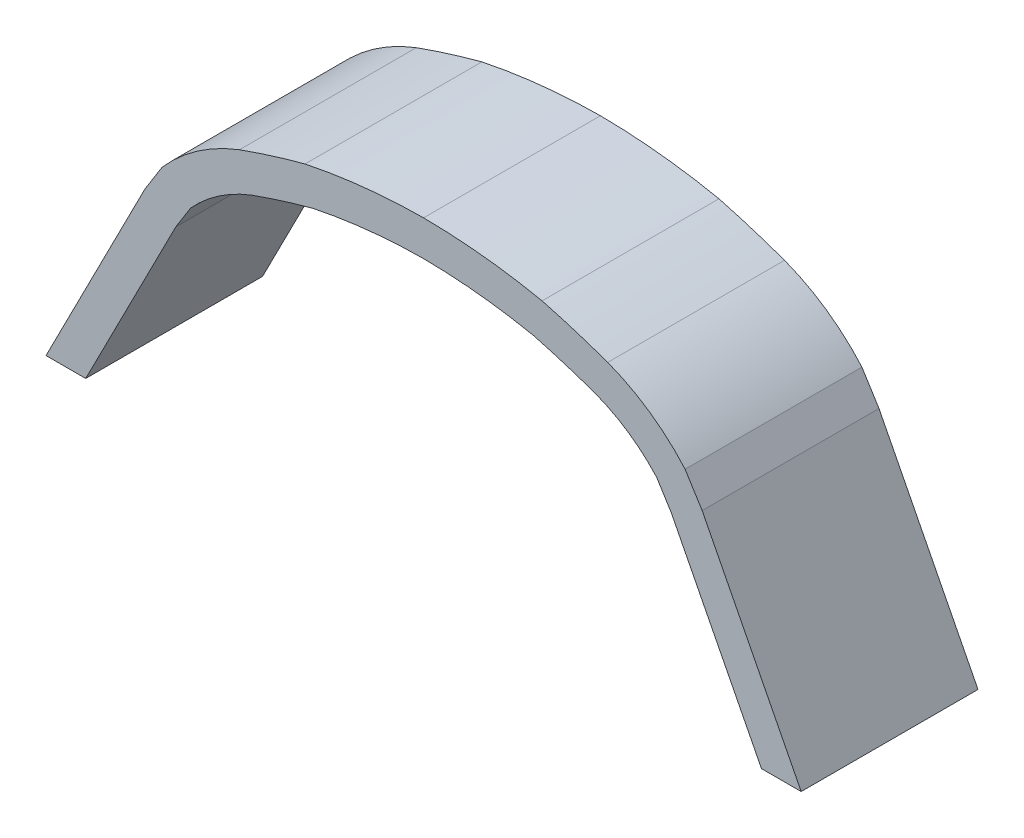
SolidWorks part; units mm, degrees
ref_plane "Front Plane" through (0, 0, 0) normal (0, 0, 1) x (1, 0, 0)
ref_plane "Top Plane" through (0, 0, 0) normal (0, 1, 0) x (1, 0, 0)
ref_plane "Right Plane" through (0, 0, 0) normal (1, 0, 0) x (0, 0, -1)
sketch "Sketch1" plane through (0, 0, 0) normal (0, 0, 1) x (1, 0, 0)
  line L0 (-4.7635, 0) -> (4.7635, 0) construction
  line L1 (-4.7635, 0) -> (-4.8535, 0) construction
  line L2 (-4.8535, 0) -> (-3.5592, 2.5338)
  line L3 (0, 0) -> (0, 3.9174) construction
  line L4 (-4.8002, 0.1044) -> (-4.7311, 0.0723) construction
  line L5 (-3.5592, 2.5338) -> (-3.3482, 2.8713)
  line L6 (-3.5592, 2.5338) -> (-3.4941, 2.4941) construction
  line L7 (-2.905, 3.159) -> (-2.9441, 3.2244) construction
  line L8 (-2.4359, 3.4045) -> (-2.4687, 3.4733) construction
  line L9 (-2.0073, 3.548) -> (-2.0301, 3.6207) construction
  line L10 (-1.5693, 3.675) -> (-1.5857, 3.7495) construction
  line L11 (-0.7917, 3.8061) -> (-0.7969, 3.8722) construction
  line L12 (3.5592, 2.5338) -> (3.3482, 2.8713)
  line L13 (-3.3482, 2.8713) -> (-3.2837, 2.8308) construction
  line L14 (4.8535, 0) -> (3.5592, 2.5338)
  line L15 (4.7635, 0) -> (4.8535, 0) construction
  line L16 (4.8535, 0) -> (5.4239, 0)
  line L17 (-5.4239, 0) -> (-4.0016, 2.7844)
  line L18 (-4.0016, 2.7844) -> (-3.7564, 3.1767)
  line L19 (4.0016, 2.7844) -> (3.7564, 3.1767)
  line L20 (5.4239, 0) -> (4.0016, 2.7844)
  line L22 (-4.8535, 0) -> (-5.4239, 0)
  line L23 (-5.6834, -0.508) -> (-4.0016, 2.7844) construction
  line L24 (-4.7635, -0.508) -> (-5.6834, -0.508) construction
  line L25 (5.6834, -0.508) -> (4.0016, 2.7844) construction
  line L26 (4.7635, -0.508) -> (5.6834, -0.508) construction
  arc A0 (-3.3482, 2.8713) -> (-2.4687, 3.4733) centre (-1.6554, 1.3414) cw
  arc A1 (-2.4687, 3.4733) -> (-1.5857, 3.7495) centre (1.2481, -6.8605) cw
  arc A2 (-1.5857, 3.7495) -> (0, 3.9174) centre (0.0631, -4.2481) cw
  arc A3 (1.5857, 3.7495) -> (0, 3.9174) centre (-0.0631, -4.2481) ccw
  arc A4 (2.4687, 3.4733) -> (1.5857, 3.7495) centre (-1.2481, -6.8605) ccw
  arc A5 (3.3482, 2.8713) -> (2.4687, 3.4733) centre (1.6554, 1.3414) ccw
  arc A6 (-3.7564, 3.1767) -> (-2.645, 3.9497) centre (-1.6554, 1.3414) cw
  arc A7 (-2.645, 3.9497) -> (-1.7027, 4.244) centre (1.2481, -6.8605) cw
  arc A8 (-1.7027, 4.244) -> (0, 4.4254) centre (0.0631, -4.2481) cw
  arc A9 (1.7027, 4.244) -> (0, 4.4254) centre (-0.0631, -4.2481) ccw
  arc A10 (2.645, 3.9497) -> (1.7027, 4.244) centre (-1.2481, -6.8605) ccw
  arc A11 (3.7564, 3.1767) -> (2.645, 3.9497) centre (1.6554, 1.3414) ccw
  spline S0 degree 3 poles (-4.7635, 0) (-4.7635, 0.0005) (-4.7636, 0.0011) (-4.7636, 0.0019) (-4.7636, 0.0022) (-4.7535, 0.024) (-4.7412, 0.0505) (-4.7267, 0.0817) (-4.7197, 0.0961) (-4.6407, 0.252) (-4.5474, 0.4361) (-4.4398, 0.6484) (-4.3897, 0.747) (-4.2916, 0.9396) (-4.2049, 1.1097) (-4.1297, 1.2572) (-4.1136, 1.288) (-4.0861, 1.339) (-4.0587, 1.39) (-4.0312, 1.441) (-4.0153, 1.4719) (-3.9452, 1.6136) (-3.8676, 1.7705) (-3.7826, 1.9425) (-3.7447, 2.019) (-3.6799, 2.1487) (-3.6232, 2.2623) (-3.5745, 2.3598) (-3.5593, 2.3872) (-3.5321, 2.4317) (-3.505, 2.4763) (-3.4778, 2.5208) (-3.4614, 2.5475) (-3.397, 2.6501) (-3.3343, 2.7501) (-3.2733, 2.8475) (-3.259, 2.8647) (-3.2248, 2.8969) (-3.1954, 2.9245) (-3.1705, 2.948) (-3.1676, 2.9507) (-3.1648, 2.9534) (-3.1625, 2.9556) (-3.161, 2.9569) (-3.1514, 2.9657) (-3.1398, 2.9762) (-3.1264, 2.9885) (-3.119, 2.9948) (-3.1057, 3.0059) (-3.0924, 3.017) (-3.0793, 3.028) (-3.0724, 3.0342) (-3.0633, 3.0446) (-3.0545, 3.0546) (-3.0461, 3.0642) (-3.0403, 3.0695) (-3.0296, 3.0771) (-3.019, 3.0848) (-3.0083, 3.0924) (-3.0021, 3.0968) (-2.9919, 3.1039) (-2.9822, 3.1106) (-2.9731, 3.117) (-2.9684, 3.1202) (-2.9617, 3.1245) (-2.9555, 3.1285) (-2.9497, 3.1322) (-2.9462, 3.1344) (-2.9314, 3.1432) (-2.9121, 3.1547) (-2.8911, 3.1673) (-2.8752, 3.1771) (-2.8603, 3.1863) (-2.846, 3.1952) (-2.8311, 3.204) (-2.8192, 3.2111) (-2.8036, 3.2204) (-2.7932, 3.2266) (-2.7831, 3.2326) (-2.76, 3.2462) (-2.735, 3.2609) (-2.7067, 3.2776) (-2.6923, 3.2852) (-2.6431, 3.3078) (-2.5899, 3.3323) (-2.5327, 3.3586) (-2.5059, 3.3711) (-2.466, 3.3901) (-2.4275, 3.4085) (-2.3904, 3.4262) (-2.3674, 3.4352) (-2.1317, 3.509) (-1.9031, 3.5806) (-1.6818, 3.6498) (-1.6801, 3.6504) (-1.6772, 3.6514) (-1.6744, 3.6524) (-1.6717, 3.6534) (-1.6703, 3.6539) (-1.6682, 3.6545) (-1.6659, 3.6551) (-1.6638, 3.6557) (-1.6619, 3.6562) (-1.6601, 3.6566) (-1.6583, 3.6569) (-1.645, 3.6595) (-1.6294, 3.6625) (-1.6113, 3.6659) (-1.6028, 3.6677) (-1.506, 3.6889) (-1.4084, 3.7104) (-1.3099, 3.732) (-1.2988, 3.7342) (-1.2803, 3.7376) (-1.2618, 3.741) (-1.2432, 3.7445) (-1.2321, 3.7463) (-1.1355, 3.7604) (-1.0223, 3.777) (-0.8926, 3.7959) (-0.8314, 3.803) (-0.7312, 3.8108) (-0.6366, 3.8181) (-0.5475, 3.825) (-0.5026, 3.8285) (-0.4423, 3.8303) (-0.3829, 3.8322) (-0.3245, 3.834) (-0.2825, 3.8351) (-0.201, 3.837) (-0.1153, 3.8391) (-0.0254, 3.8413) (0.0292, 3.8412) (0.1211, 3.8389) (0.2093, 3.8366) (0.2936, 3.8345) (0.3368, 3.8334) (0.3962, 3.8315) (0.4561, 3.8296) (0.5166, 3.8276) (0.5612, 3.8241) (0.6495, 3.8171) (0.7432, 3.8096) (0.8423, 3.8018) (0.9028, 3.7947) (1.0326, 3.7755) (1.145, 3.759) (1.24, 3.7449) (1.2481, 3.7436) (1.2696, 3.7396) (1.2894, 3.7359) (1.3074, 3.7326) (1.3101, 3.732) (1.4049, 3.7112) (1.5019, 3.6898) (1.6008, 3.6681) (1.6097, 3.6662) (1.6286, 3.6626) (1.6448, 3.6595) (1.6586, 3.6568) (1.6604, 3.6564) (1.6623, 3.656) (1.6643, 3.6556) (1.6665, 3.655) (1.6691, 3.6542) (1.6714, 3.6535) (1.7859, 3.6227) (1.9031, 3.5912) (2.0236, 3.5588) (2.0343, 3.5553) (2.0517, 3.5488) (2.0691, 3.5423) (2.0866, 3.5358) (2.097, 3.532) (2.1688, 3.5065) (2.2556, 3.4758) (2.3574, 3.4396) (2.4112, 3.4149) (2.5347, 3.3534) (2.6432, 3.2993) (2.7369, 3.2526) (2.7449, 3.2483) (2.7582, 3.2409) (2.7714, 3.2335) (2.7847, 3.2262) (2.7925, 3.2216) (2.8055, 3.214) (2.8184, 3.2064) (2.8313, 3.1988) (2.8391, 3.1943) (2.8686, 3.1781) (2.8977, 3.1621) (2.9265, 3.1463) (2.9331, 3.1424) (2.9465, 3.1339) (2.9582, 3.1265) (2.9682, 3.1202) (2.9696, 3.1193) (2.972, 3.1177) (2.9744, 3.1161) (2.9768, 3.1145) (2.9782, 3.1136) (2.9847, 3.1089) (2.9923, 3.1035) (3.0007, 3.0974) (3.0049, 3.0944) (3.0199, 3.0836) (3.0363, 3.0718) (3.0541, 3.0589) (3.0624, 3.0527) (3.0749, 3.0427) (3.0872, 3.0329) (3.0992, 3.0232) (3.1061, 3.0163) (3.1171, 3.0036) (3.1278, 2.9912) (3.1382, 2.9792) (3.1437, 2.9729) (3.1524, 2.9648) (3.1621, 2.9558) (3.1714, 2.9471) (3.1979, 2.9222) (3.2268, 2.8951) (3.2594, 2.8644) (3.2735, 2.8471) (3.3341, 2.7484) (3.3961, 2.6472) (3.4598, 2.5435) (3.4762, 2.5172) (3.504, 2.4736) (3.5317, 2.4301) (3.5594, 2.3865) (3.5747, 2.3595) (3.7211, 2.0646) (3.868, 1.7685) (4.0155, 1.4713) (4.0315, 1.4404) (4.0589, 1.3895) (4.0863, 1.3385) (4.1137, 1.2876) (4.1299, 1.2568) (4.2048, 1.1102) (4.2785, 0.966) (4.351, 0.8241) (4.3631, 0.8003) (4.3831, 0.7604) (4.4031, 0.7206) (4.4231, 0.6808) (4.4352, 0.657) (4.5332, 0.4635) (4.6293, 0.2737) (4.7236, 0.0875) (4.73, 0.0744) (4.7432, 0.0458) (4.7545, 0.0215) (4.7637, 0.0016) (4.7638, 0.0013) (4.7636, 0.0008) (4.7635, 0.0004) (4.7635, 0) knots 0 0 0 0 0.000114 0.000139 0.000163 0.000188 0.005495 0.006683 0.00787 0.009058 0.045702 0.053934 0.062166 0.070398 0.102182 0.104767 0.107352 0.109938 0.117693 0.120278 0.122863 0.125448 0.15557 0.16192 0.168271 0.174621 0.194283 0.19661 0.198938 0.201265 0.208253 0.210582 0.212911 0.215241 0.237617 0.239254 0.240891 0.242528 0.249738 0.249884 0.250175 0.250611 0.250756 0.250901 0.251047 0.253665 0.254387 0.255109 0.25583 0.258271 0.258959 0.259648 0.260336 0.262039 0.262615 0.263191 0.263768 0.265546 0.266115 0.266684 0.267253 0.268888 0.269313 0.269739 0.270164 0.271082 0.271388 0.271693 0.271999 0.275236 0.276713 0.277452 0.279421 0.280615 0.281211 0.283272 0.283722 0.285258 0.285982 0.286344 0.291246 0.292455 0.293663 0.294872 0.304543 0.306736 0.308929 0.311122 0.316623 0.318451 0.32028 0.322109 0.373592 0.373729 0.373865 0.374002 0.374411 0.374523 0.374635 0.374746 0.375009 0.375164 0.375241 0.375444 0.375579 0.375647 0.378467 0.379116 0.379765 0.380415 0.401227 0.402069 0.40291 0.403751 0.406275 0.407117 0.407958 0.408799 0.4289 0.433481 0.438062 0.442643 0.455904 0.459246 0.462588 0.46593 0.472724 0.475848 0.478971 0.482095 0.494044 0.498103 0.502162 0.506221 0.518634 0.521844 0.525055 0.528265 0.535112 0.538439 0.541765 0.545092 0.558208 0.56274 0.567271 0.571802 0.592016 0.592626 0.593237 0.593848 0.597517 0.597721 0.597926 0.59813 0.619402 0.620077 0.620752 0.621428 0.624362 0.624432 0.624571 0.62478 0.624859 0.625018 0.625288 0.625467 0.625557 0.651744 0.652574 0.653404 0.654233 0.656725 0.657556 0.658387 0.659217 0.674546 0.678937 0.683328 0.68772 0.70972 0.710398 0.711075 0.711752 0.713785 0.714459 0.715132 0.715805 0.717813 0.718482 0.719151 0.71982 0.725994 0.726567 0.727139 0.727712 0.730099 0.730226 0.730354 0.730482 0.730865 0.730992 0.73112 0.731247 0.732795 0.733182 0.733568 0.733955 0.737305 0.738078 0.738851 0.739623 0.741641 0.742359 0.743078 0.743796 0.746109 0.746729 0.747348 0.747968 0.749378 0.750319 0.750789 0.757512 0.759149 0.760785 0.762421 0.784977 0.787282 0.789587 0.791893 0.798809 0.801111 0.803413 0.805715 0.874602 0.877185 0.879767 0.88235 0.890099 0.892682 0.895265 0.897848 0.929427 0.931416 0.933405 0.935394 0.941361 0.94335 0.945339 0.947328 0.991739 0.992825 0.993912 0.994999 0.999863 0.999881 0.999898 0.999916 1 1 1 1 construction
  point P2 (0, 0)
  point P8 (0, 3.8412)
  point P23 (-0.7969, 3.8722)
  point P27 (-2.9441, 3.2244)
  point P29 (-2.0301, 3.6207)
  dimension "D2" = 0.0762
  dimension "D3" = 0.508
  dimension "D1" = 0.0762
extrude "Boss-Extrude1" add sketch "Sketch1" along normal blind 2.54
